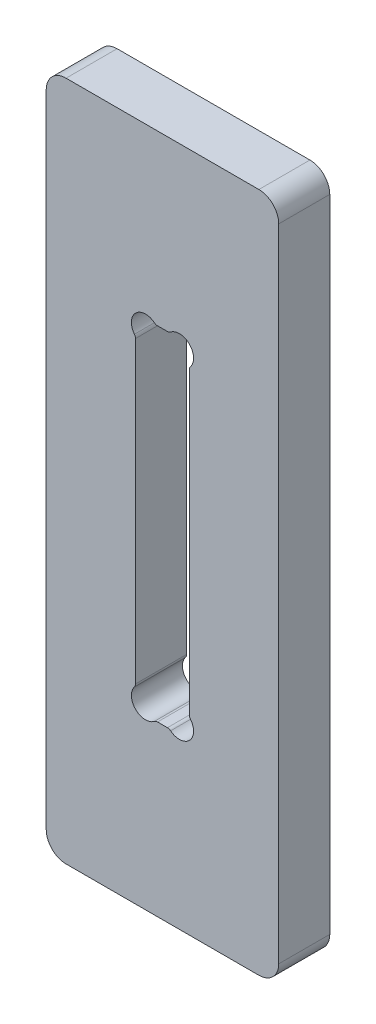
SolidWorks part; units mm, degrees
ref_plane "Front Plane" through (0, 0, 0) normal (0, 0, 1) x (1, 0, 0)
ref_plane "Top Plane" through (0, 0, 0) normal (0, 1, 0) x (1, 0, 0)
ref_plane "Right Plane" through (0, 0, 0) normal (1, 0, 0) x (0, 0, -1)
sketch "Sketch1" plane through (0, 0, 0) normal (0, 0, 1) x (1, 0, 0)
  line L1 (0, 0) -> (82, 0)
  line L2 (0, 0) -> (0, 240)
  line L3 (0, 240) -> (82, 240)
  line L4 (82, 0) -> (82, 240)
  dimension "D1" = 82
  dimension "D2" = 240
extrude "Boss-Extrude1" add sketch "Sketch1" along normal blind 18
sketch "Sketch2" plane through (0, 0, 0) normal (0, 0, 1) x (1, 0, 0)
  line L0 (41, 0) -> (41, 59.5) construction
  line L1 (0, 0) -> (82, 0) construction
  line L3 (39.2512, 59.5) -> (42.7488, 59.5)
  line L4 (31.5, 67.2512) -> (31.5, 172.7488)
  line L5 (31.5, 120) -> (41, 120) construction
  line L7 (41, 120) -> (41, 59.5) construction
  line L8 (82, 0) -> (82, 240) construction
  line L9 (31.5, 59.5) -> (41, 69) construction
  line L10 (50.5, 67.2512) -> (50.5, 172.7488)
  line L11 (39.2512, 180.5) -> (42.7488, 180.5)
  arc A0 (31.1123, 66.1353) -> (38.1353, 59.1123) centre (35.0355, 63.0355) ccw
  arc A1 (31.1123, 66.1353) -> (31.5, 67.2512) centre (29.7, 67.2512) ccw
  arc A2 (38.1353, 59.1123) -> (39.2512, 59.5) centre (39.2512, 57.7) cw
  arc A3 (50.8877, 66.1353) -> (50.5, 67.2512) centre (52.3, 67.2512) cw
  arc A4 (50.8877, 66.1353) -> (43.8647, 59.1123) centre (46.9645, 63.0355) cw
  arc A5 (43.8647, 59.1123) -> (42.7488, 59.5) centre (42.7488, 57.7) ccw
  arc A6 (31.1123, 173.8647) -> (31.5, 172.7488) centre (29.7, 172.7488) cw
  arc A7 (31.1123, 173.8647) -> (38.1353, 180.8877) centre (35.0355, 176.9645) cw
  arc A8 (38.1353, 180.8877) -> (39.2512, 180.5) centre (39.2512, 182.3) ccw
  arc A9 (43.8647, 180.8877) -> (42.7488, 180.5) centre (42.7488, 182.3) cw
  arc A10 (50.8877, 173.8647) -> (43.8647, 180.8877) centre (46.9645, 176.9645) ccw
  arc A11 (50.8877, 173.8647) -> (50.5, 172.7488) centre (52.3, 172.7488) ccw
  point P3 (41, 0)
  point P8 (82, 120)
  point P21 (41, 59.5)
  point P42 (50.5, 120)
  dimension "D7" = 5
  dimension "D4" = 1.8
  dimension "D1" = 45
  dimension "D2" = 60.5
  dimension "D3" = 9.5
extrude "Cut-Extrude1" cut sketch "Sketch2" along normal through all
fillet "Fillet1" radius 7 4 edges at (0, 0, 9) (0, 240, 9) (82, 0, 9) (82, 240, 9)
equation "\"tool_diameter\"=9"
equation "\"hole_clearance\"=0.5"
equation "\"material_thickness\"=18"
equation "\"clearance\"=0.5"
equation "\"outer_slot\"=0.5"
equation "\"fillet\"=7"
equation "\"D1@Sketch1\"=100-\"material_thickness\""
equation "\"D1@Boss-Extrude1\"=\"material_thickness\""
equation "\"D2@Sketch2\"=60+\"clearance\""
equation "\"D7@Sketch2\"=\"tool_diameter\"/2+\"hole_clearance\""
equation "\"D3@Sketch2\"=\"material_thickness\"/2+\"clearance\""
equation "\"D4@Sketch2\"=\"material_thickness\"/10"
equation "\"D1@Fillet1\"=\"fillet\""
equation "\"string\"= 2 * \"tool_diameter\" / 2 * cos ( 45deg )"
equation "\"angle\"= IIF ( \"string\" < \"limit\" , 45 , ( 180 - 2 * arcsin ( \"ThicknessVStool_dia\" ) ) / 2 )"
equation "\"limit\"= \"material_thickness\" / 2 * 9 / 10"
equation "\"ThicknessVStool_dia\"= IIF ( \"limit\" / \"tool_diameter\" > 1 , 1 , \"limit\" / \"tool_diameter\" )"
equation "\"D1@Sketch2\"=\"angle\""
